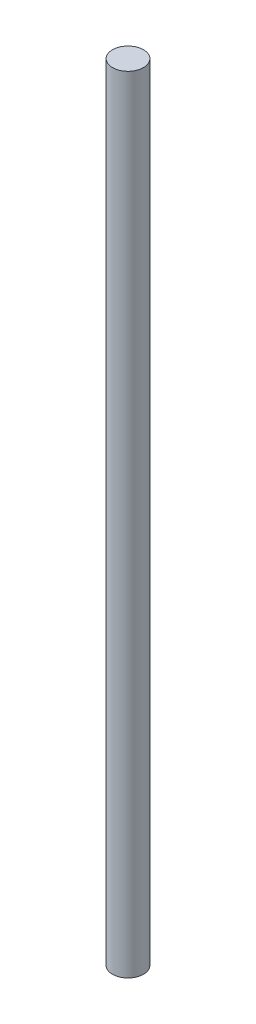
SolidWorks part; units mm, degrees
ref_plane "Front Plane" through (0, 0, 0) normal (0, 0, 1) x (1, 0, 0)
ref_plane "Top Plane" through (0, 0, 0) normal (0, 1, 0) x (1, 0, 0)
ref_plane "Right Plane" through (0, 0, 0) normal (1, 0, 0) x (0, 0, -1)
sketch "Sketch1" plane through (0, 0, 0) normal (0, 1, 0) x (1, 0, 0)
  circle A0 centre (0, 0) radius 4.7625
extrude "Boss-Extrude1" add sketch "Sketch1" along normal blind 241.3
